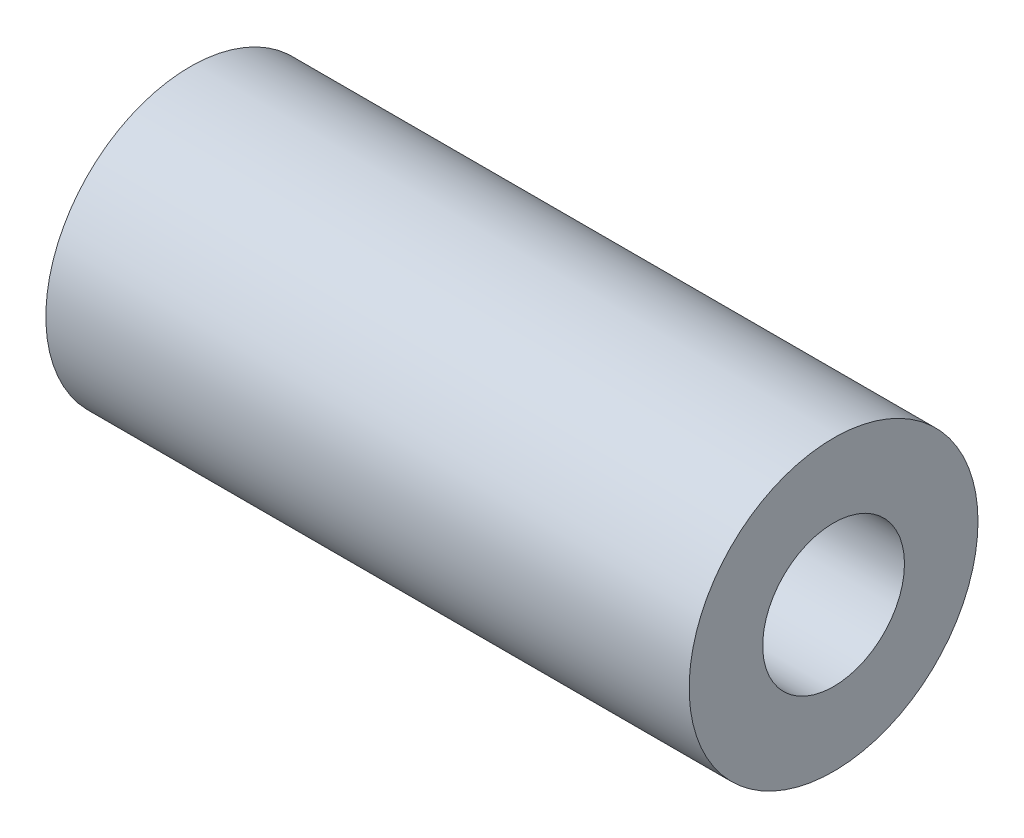
SolidWorks part; units mm, degrees
ref_plane "前视基准面" through (0, 0, 0) normal (0, 0, 1) x (1, 0, 0)
ref_plane "上视基准面" through (0, 0, 0) normal (0, 1, 0) x (1, 0, 0)
ref_plane "右视基准面" through (0, 0, 0) normal (1, 0, 0) x (0, 0, -1)
sketch "草图1" plane through (0, 0, 0) normal (1, 0, 0) x (0, 0, -1)
  circle A0 centre (0, 0) radius 2.7
  circle A1 centre (0, 0) radius 5.5
  dimension "D1" = 5.4
  dimension "D2" = 11
extrude "凸台-拉伸1" add sketch "草图1" along normal blind 24.5
